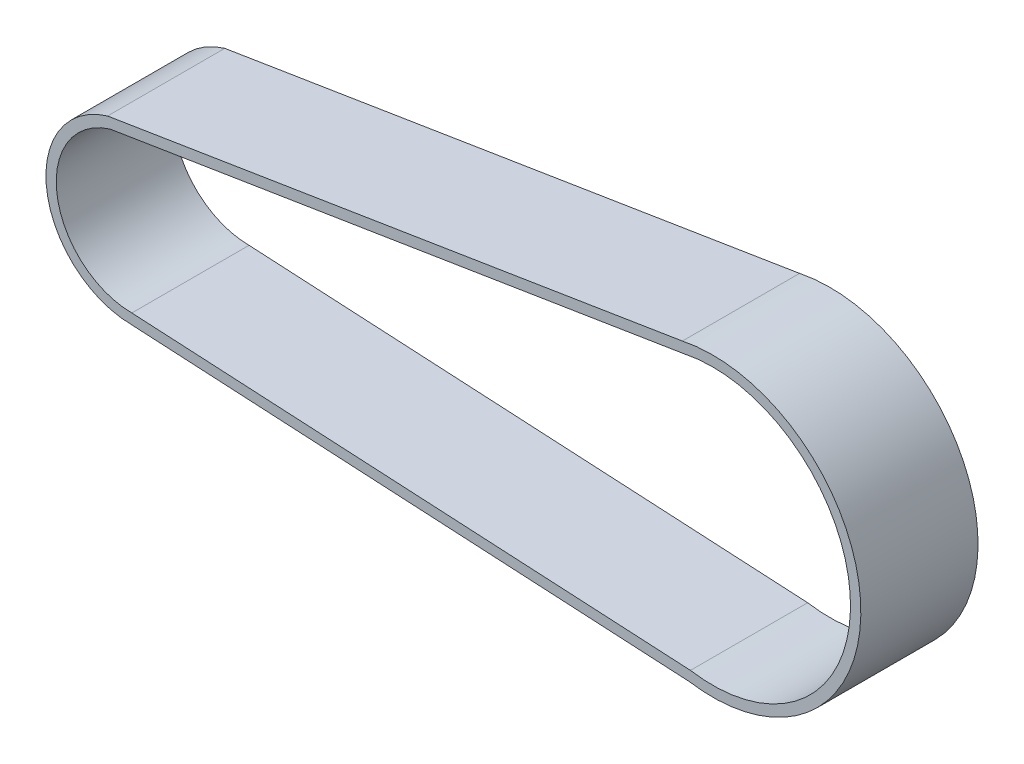
SolidWorks part; units mm, degrees
material "Rubber"
ref_plane "Front Plane" through (0, 0, 0) normal (0, 0, 1) x (1, 0, 0)
ref_plane "Top Plane" through (0, 0, 0) normal (0, 1, 0) x (1, 0, 0)
ref_plane "Right Plane" through (0, 0, 0) normal (1, 0, 0) x (0, 0, -1)
sketch "Sketch1" plane through (0, 0, 0) normal (0, 0, 1) x (1, 0, 0)
  line L0 (-3.216, 10.5194) -> (80.0949, 23.9263)
  line L5 (80.9957, -15.385) -> (-0.0332, -10.9999)
  line L6 (-3.5528, 11.9845) -> (79.8218, 25.4017)
  line L7 (80.8355, -16.8785) -> (-0.0773, -12.4998)
  arc A4 (-3.216, 10.5194) -> (-0.0332, -10.9999) centre (0, 0) ccw
  arc A5 (80.9957, -15.385) -> (80.0949, 23.9263) centre (84.2121, 4.3547) ccw
  arc A6 (80.8355, -16.8785) -> (79.8218, 25.4017) centre (84.2121, 4.3547) ccw
  arc A7 (-3.5528, 11.9845) -> (-0.0773, -12.4998) centre (0, 0) ccw
  point P6 (81.033, 18.3324)
  point P14 (80.836, -15.3839)
  point P15 (-3.5528, 10.5194)
  dimension "D1" = 267
  dimension "D2" = 20
  dimension "D3" = 11
  dimension "D4" = 1.5
extrude "Boss-Extrude1" add sketch "Sketch1" along normal blind 17
